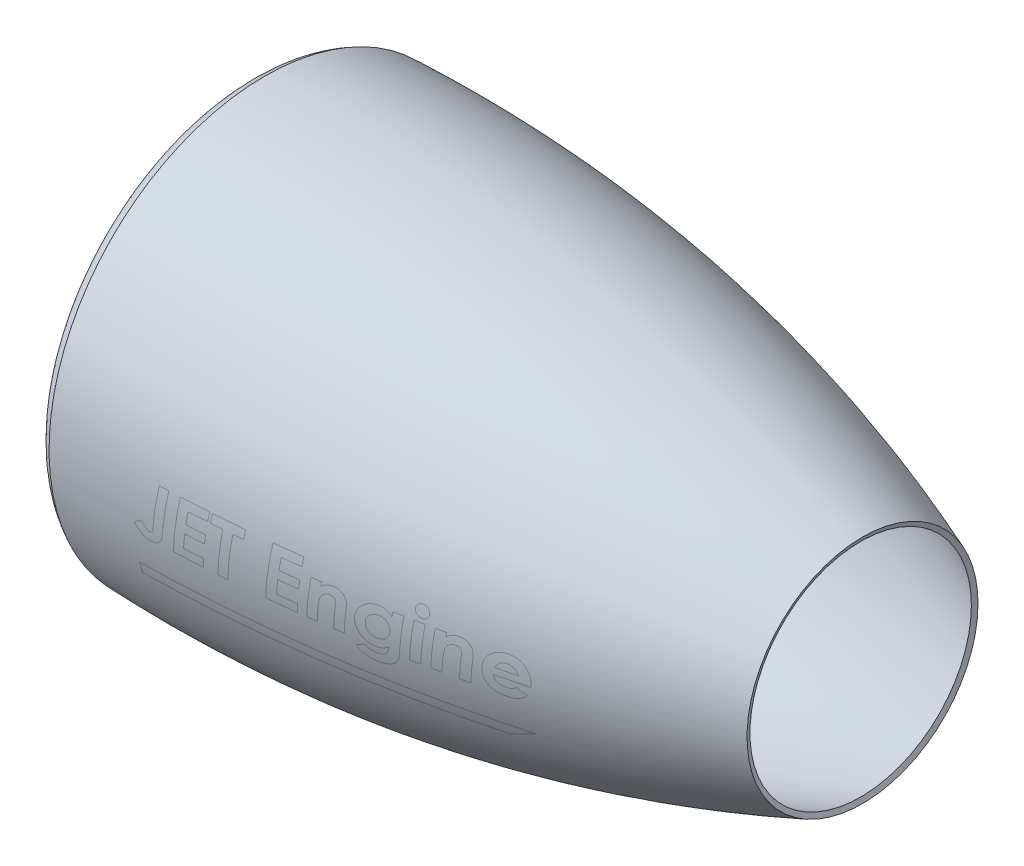
SolidWorks part; units mm, degrees
ref_plane "Front Plane" through (0, 0, 0) normal (0, 0, 1) x (1, 0, 0)
ref_plane "Top Plane" through (0, 0, 0) normal (0, 1, 0) x (1, 0, 0)
ref_plane "Right Plane" through (0, 0, 0) normal (1, 0, 0) x (0, 0, -1)
sketch "Sketch1" plane through (0, 0, 0) normal (0, 0, 1) x (1, 0, 0)
  line L0 (0, 0) -> (664.6623, 0) construction
  line L1 (0, 0) -> (0, 205.4814) construction
  line L2 (0, 180) -> (25, 180)
  line L3 (25, 180) -> (34.4623, 190)
  line L4 (34.4623, 190) -> (59.4623, 190)
  spline S0 degree 2 poles (0, 205.4814) (299.7035, 217.0258) (580, 108) knots 0 0 0 1 1 1
  spline S1 degree 3 poles (0, 205.4814) (-11.0036, 199.8483) (-10.9295, 190.3567) (-6.9752, 182.6951) (0, 180) knots 0 0 0 0 0.576018 1 1 1 1
  dimension "D1" = 580
  dimension "D2" = 108
  dimension "D3" = 180
  dimension "D4" = 190
  dimension "D5" = 25
  dimension "D6" = 25
surface "Surface-Revolve1" sketch "Sketch1" parameters "D1"=360
thicken "Thicken1" thickness 5 parameters "D1"=5
ref_plane "Plane1" through (0, 0, 250) normal (0, 0, 1) x (1, 0, 0)
sketch "Sketch2" plane through (0, 0, 250) normal (0, 0, 1) x (1, 0, 0)
  line L0 (419.2979, -57.7845) -> (395.9588, -68.3427)
  line L1 (79.7689, -57.7845) -> (419.2979, -57.7845)
  line L2 (79.7689, -57.7845) -> (79.7689, -68.3427)
  line L3 (79.7689, -68.3427) -> (395.9588, -68.3427)
  text T0 "<i>JET Engine </i>" font "Century Gothic" height 50
split line "Split Line1"
